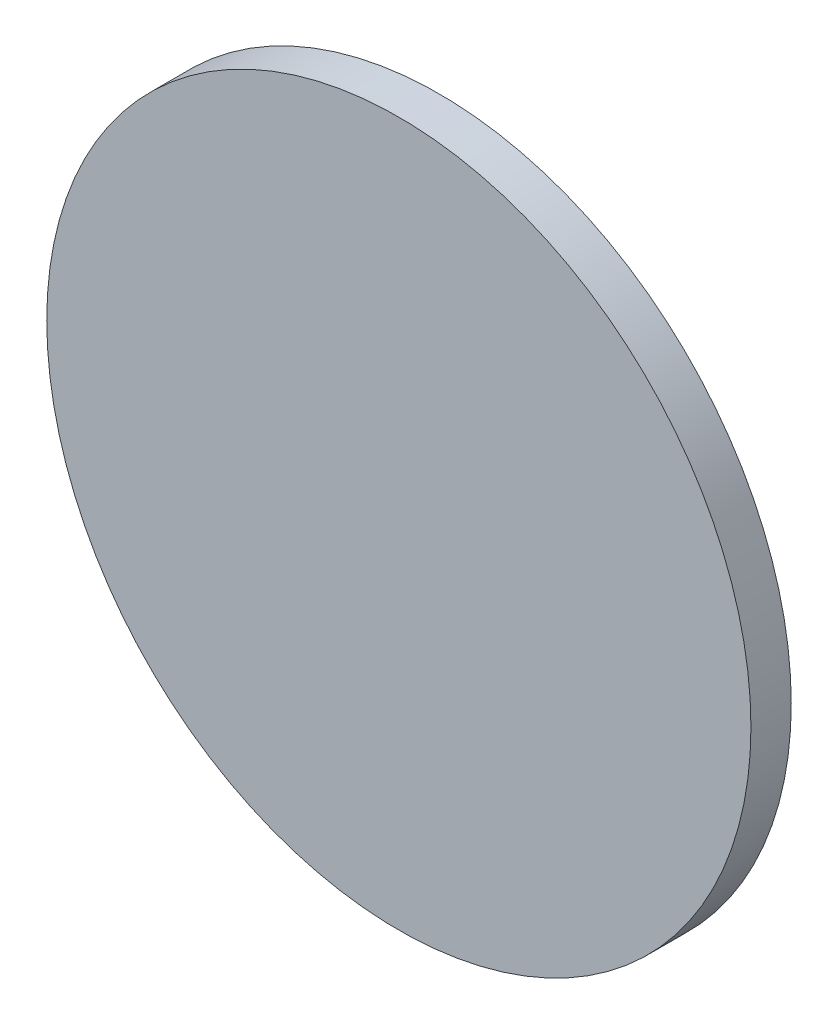
SolidWorks part; units mm, degrees
material "Corrugated Paper"
ref_plane "Front Plane" through (0, 0, 0) normal (0, 0, 1) x (1, 0, 0)
ref_plane "Top Plane" through (0, 0, 0) normal (0, 1, 0) x (1, 0, 0)
ref_plane "Right Plane" through (0, 0, 0) normal (1, 0, 0) x (0, 0, -1)
sketch "Croquis1" plane through (0, 0, 0) normal (0, 0, 1) x (1, 0, 0)
  circle A0 centre (0, 0) radius 26.2
  dimension "D1" = 52.4
extrude "Saliente-Extruir1" add sketch "Croquis1" along normal blind 3
equation "\"ODablative\"= 52.4"
equation "\"D1@Croquis1\"=\"ODablative\""
equation "\"ThicknessAblative\"=3"
equation "\"D1@Saliente-Extruir1\"=\"ThicknessAblative\""
